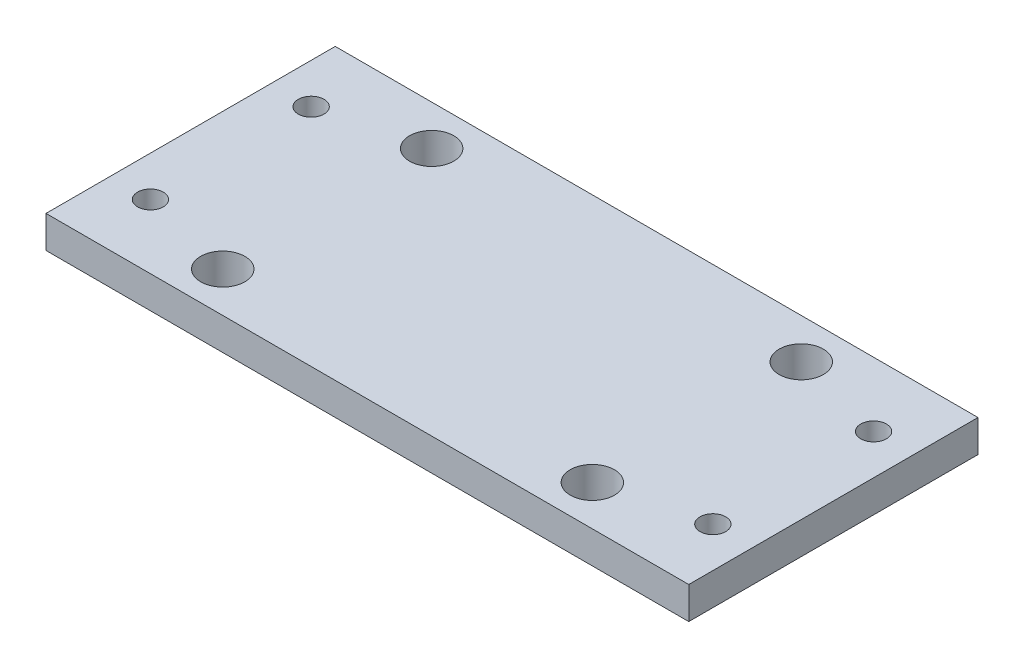
SolidWorks part; units mm, degrees
ref_plane "前视基准面" through (0, 0, 0) normal (0, 0, 1) x (1, 0, 0)
ref_plane "上视基准面" through (0, 0, 0) normal (0, 1, 0) x (1, 0, 0)
ref_plane "右视基准面" through (0, 0, 0) normal (1, 0, 0) x (0, 0, -1)
sketch "草图1" plane through (0, 0, 0) normal (0, 1, 0) x (1, 0, 0)
  line L0 (-29.9191, 27.4812) -> (16.0809, 27.4812) construction
  line L1 (-29.9191, 1.4812) -> (-29.9191, 27.4812) construction
  line L2 (-29.9191, 1.4812) -> (16.0809, 1.4812) construction
  line L3 (16.0809, 1.4812) -> (16.0809, 27.4812) construction
  line L4 (-6.9191, 27.4812) -> (-6.9191, 1.4812) construction
  line L5 (-29.9191, 14.4812) -> (16.0809, 14.4812) construction
  line L6 (-34.9191, 32.4812) -> (33.0809, 32.4812)
  line L8 (-29.9191, 14.4812) -> (-51.9173, 14.4812) construction
  line L9 (-6.9191, 27.4812) -> (-6.9191, 42.3041) construction
  line L10 (-34.9191, -3.5188) -> (33.0809, -3.5188)
  line L12 (-34.9191, 32.4812) -> (-46.9191, 32.4812)
  line L13 (-46.9191, 32.4812) -> (-46.9191, -3.5188)
  line L14 (-46.9191, -3.5188) -> (-34.9191, -3.5188)
  line L15 (33.0809, 32.4812) -> (33.0809, -3.5188)
  circle A0 centre (-29.9191, 27.4812) radius 2.75
  circle A1 centre (16.0809, 27.4812) radius 2.75
  circle A2 centre (-29.9191, 1.4812) radius 2.75
  circle A3 centre (16.0809, 1.4812) radius 2.75
  circle A4 centre (-41.9191, 24.4812) radius 1.6
  circle A5 centre (28.0809, 24.4812) radius 1.6
  circle A6 centre (-41.9191, 4.4812) radius 1.6
  circle A7 centre (28.0809, 4.4812) radius 1.6
  point P18 (-34.9191, 14.4812)
  point P20 (-6.9191, -3.5188)
  point P21 (-6.9191, 32.4812)
  point P25 (0, 0)
  dimension "D1" = 5.5
  dimension "D2" = 5.5
  dimension "D4" = 40
  dimension "D7" = 35
  dimension "D8" = 10
  dimension "D9" = 3.2
  dimension "D3" = 46
  dimension "D5" = 40
  dimension "D6" = 26
extrude "凸台-拉伸1" add sketch "草图1" along normal blind 4
